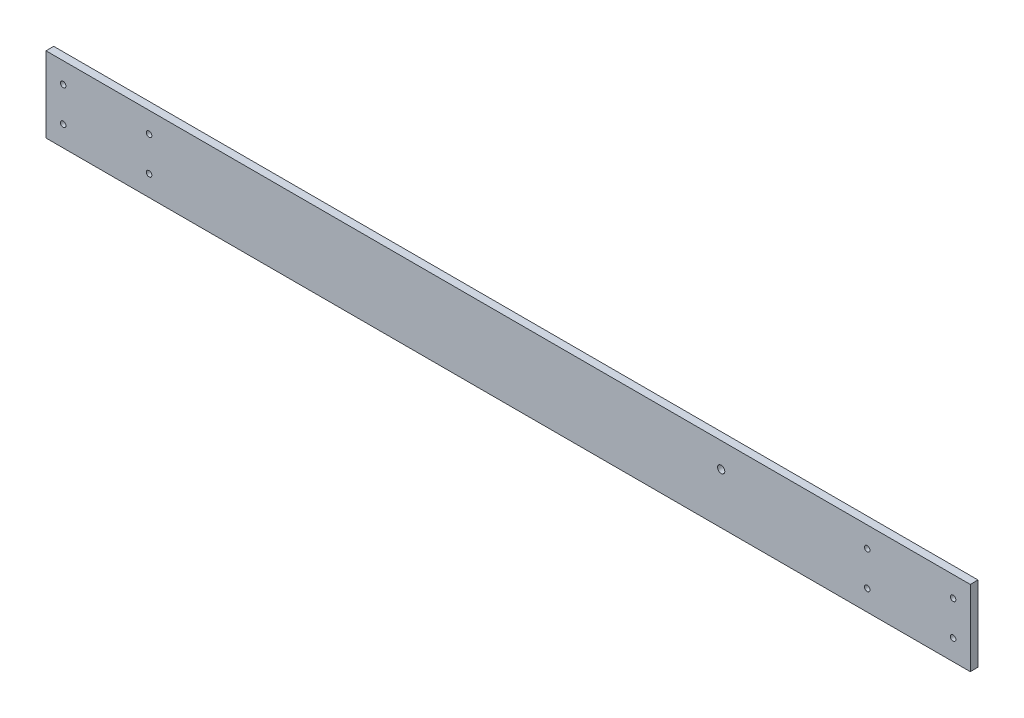
SolidWorks part; units mm, degrees
ref_plane "Front Plane" through (0, 0, 0) normal (0, 0, 1) x (1, 0, 0)
ref_plane "Top Plane" through (0, 0, 0) normal (0, 1, 0) x (1, 0, 0)
ref_plane "Right Plane" through (0, 0, 0) normal (1, 0, 0) x (0, 0, -1)
sketch "Sketch2" plane through (0, 0, 0) normal (0, 0, 1) x (1, 0, 0)
  line L0 (269, 0) -> (149, 0) construction
  line L1 (-269, -22) -> (269, -22)
  line L2 (-269, -22) -> (-269, 22)
  line L3 (-269, 22) -> (269, 22)
  line L4 (269, -22) -> (269, 22)
  line L5 (-269, -22) -> (269, 22) construction
  line L6 (-269, 22) -> (269, -22) construction
  line L7 (149, -1) -> (149, 9) construction
  line L8 (269, 3.3321) -> (269, 22) construction
  line L9 (0, 0) -> (0, 11.9613) construction
  circle A0 centre (124, 7.5) radius 2.1 construction
  circle A1 centre (124, 7.5) radius 2.1
  circle A2 centre (259, 10) radius 1.6
  circle A3 centre (209, 10) radius 1.6
  circle A6 centre (209, -10) radius 1.6
  circle A9 centre (259, -10) radius 1.6
  circle A10 centre (-209, 10) radius 1.6
  circle A11 centre (-209, -10) radius 1.6
  circle A12 centre (-259, -10) radius 1.6
  circle A13 centre (-259, 10) radius 1.6
  point P0 (0, 0)
  dimension "D3" = 10
  dimension "D5" = 3.2
  dimension "D1" = 44
  dimension "D2" = 538
  dimension "D4" = 10
  dimension "D6" = 2
  dimension "D7" = 2
extrude "Boss-Extrude1" add sketch "Sketch2" along normal blind 4.5
